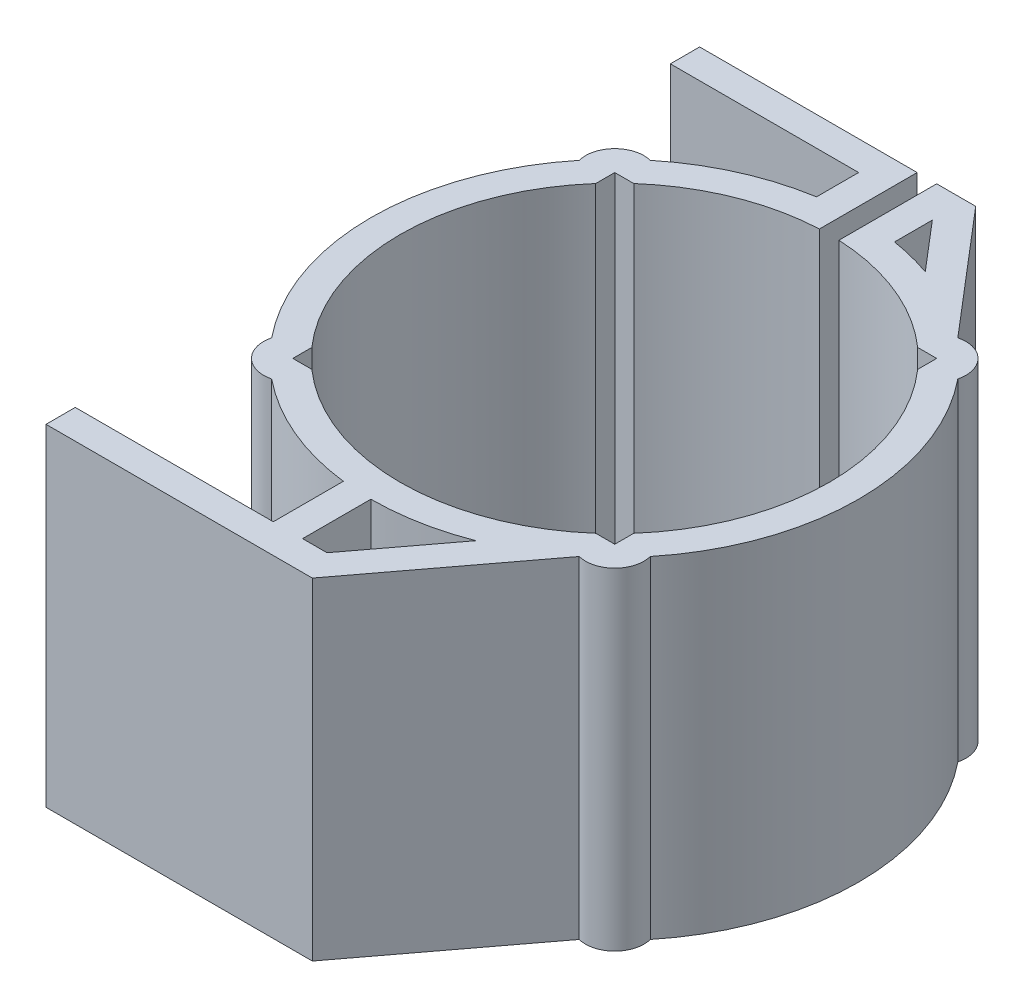
SolidWorks part; units mm, degrees
ref_plane "Front Plane" through (0, 0, 0) normal (0, 0, 1) x (1, 0, 0)
ref_plane "Top Plane" through (0, 0, 0) normal (0, 1, 0) x (1, 0, 0)
ref_plane "Right Plane" through (0, 0, 0) normal (1, 0, 0) x (0, 0, -1)
sketch "Sketch1" plane through (0, 0, 0) normal (0, 1, 0) x (1, 0, 0)
  line L0 (0, 0) -> (0, 16.5) construction
  line L1 (0, 16.5) -> (16.5, 16.5) construction
  line L2 (16.5, 16.5) -> (-16.5, -16.5) construction
  line L3 (0, 22) -> (0, 32) construction
  line L4 (16.5, 16.5) -> (-16.5, 16.5)
  line L5 (16.5, 16.5) -> (16.5, -16.5)
  line L6 (16.5, -16.5) -> (-16.5, -16.5)
  line L7 (-16.5, 16.5) -> (-16.5, -16.5)
  line L8 (1, 22) -> (1, 32)
  line L9 (-1, 22) -> (-1, 32)
  line L10 (1, 32) -> (5, 32)
  line L11 (5, 32) -> (15.7595, 19.4072)
  line L12 (18.6213, 18.6213) -> (16.5, 16.5) construction
  line L13 (4, 22) -> (4, 28.5521)
  line L14 (4, 28.5521) -> (4, 28.5521)
  line L15 (4, 28.5521) -> (13.4787, 17.4584)
  line L16 (15.7595, -19.4072) -> (4, -35)
  line L17 (0, 0) -> (0, -25) construction
  line L18 (0, -25) -> (0, -35) construction
  line L19 (0, -35) -> (4, -35)
  line L20 (0, -35) -> (-23.2995, -35)
  line L21 (-1, 32) -> (-23.2995, 32)
  line L22 (0, -32) -> (-23.2995, -32)
  line L23 (0, -32) -> (2.505, -32)
  line L24 (13.3643, -17.6008) -> (2.505, -32)
  line L25 (-4, 22) -> (-4, 29)
  line L26 (-4, 29) -> (-23.2995, 29)
  line L27 (-23.2995, 32) -> (-23.2995, 29)
  line L28 (-23.2995, -32) -> (-23.2995, -35)
  line L29 (0, -32) -> (0, -25)
  line L30 (-3, -32) -> (-3, -24.8193)
  line L31 (1, 22) -> (1, 21.9773)
  line L32 (-1, 22) -> (-1, 21.9773)
  circle A0 centre (0, 0) radius 25
  circle A1 centre (0, 0) radius 22
  arc A2 (-15.7595, 19.4072) -> (-19.4072, 15.7595) centre (-16.5, 16.5) ccw
  arc A3 (19.4072, 15.7595) -> (15.7595, 19.4072) centre (16.5, 16.5) ccw
  arc A4 (15.7595, -19.4072) -> (19.4072, -15.7595) centre (16.5, -16.5) ccw
  arc A5 (-19.4072, -15.7595) -> (-15.7595, -19.4072) centre (-16.5, -16.5) ccw
  point P24 (0, 0)
  dimension "D1" = 50
  dimension "D6" = 3
  dimension "D3" = 16.5
  dimension "D4" = 16.5
  dimension "D5" = 46.669
  dimension "D8" = 10
  dimension "D11" = 4
  dimension "D13" = 10
  dimension "D16" = 3
  dimension "D2" = 3
  dimension "D9" = 1
  dimension "D10" = 1
  dimension "D12" = 3
  dimension "D14" = 3
  dimension "D15" = 3
  dimension "D7" = 4
extrude "Boss-Extrude1" add sketch "Sketch1" along normal blind 34
ref_plane "Plane1" through (19.4072, 0, 0) normal (-1, 0, 0) x (0, 0, 1)
sketch "Sketch4" plane through (4, 0, 0) normal (1, 0, 0) x (0, 0, -1)
  line L5 (24.6779, 23) -> (28.5521, 23)
  line L6 (24.6779, 23) -> (24.6779, 11)
  line L7 (24.6779, 11) -> (28.5521, 11)
  line L8 (24.6779, 0) -> (28.5521, 0)
  line L9 (28.5521, 0) -> (28.5521, 34)
  line L10 (28.5521, 34) -> (24.6779, 34)
  line L11 (24.6779, 34) -> (24.6779, 0)
  line L12 (24.6779, 0) -> (28.5521, 0) construction
  line L13 (28.5521, 0) -> (28.5521, 34) construction
  line L14 (28.5521, 34) -> (24.6779, 34) construction
  line L15 (24.6779, 34) -> (24.6779, 0) construction
  line L16 (28.5521, 23) -> (28.5521, 11)
  point P6 (24.6779, 17)
  point P10 (0, 0)
  dimension "D2" = 12
  dimension "D1" = 0
ref_plane "Plane2" through (0, 23, 0) normal (0, -1, 0) x (0, 0, -1)
ref_plane "Plane3" through (0, 11, 0) normal (0, -1, 0) x (0, 0, -1)
sketch "Sketch6" plane through (0, 23, 0) normal (0, -1, 0) x (0, 0, -1)
  line L0 (30.7174, 3.9637) -> (22.7854, 3.9637)
  line L1 (22.7854, 3.9637) -> (22.7854, 10.6041)
  line L2 (22.7854, 10.6041) -> (30.7174, 3.9637)
  point P0 (22.7854, 10.6041)
extrude "Boss-Extrude3" add sketch "Sketch6" along normal up to surface (12 mm away) up to plane "Plane3"
sketch "Sketch3" plane through (19.4072, 0, 0) normal (-1, 0, 0) x (0, 0, 1)
  line L0 (-32, 17) -> (-27, 17) construction
  line L1 (-32, 34) -> (-32, 0) construction
  line L2 (-27, 17) -> (-27, 13) construction
  line L3 (-32, 17) -> (-32, 21) construction
  line L5 (-32, 21) -> (-27, 21)
  line L6 (-32, 21) -> (-32, 13)
  line L7 (-32, 13) -> (-27, 13)
  line L8 (-27, 21) -> (-27, 13)
  circle A0 centre (-27, 17) radius 4
  dimension "D1" = 5
  dimension "D2" = 4
  dimension "D3" = 4
extrude "Cut-Extrude1" cut sketch "Sketch3" along normal up to vertex (14.4072 mm away) contours L8 A0 | L8 A0 | A0 L5 L6 L7
